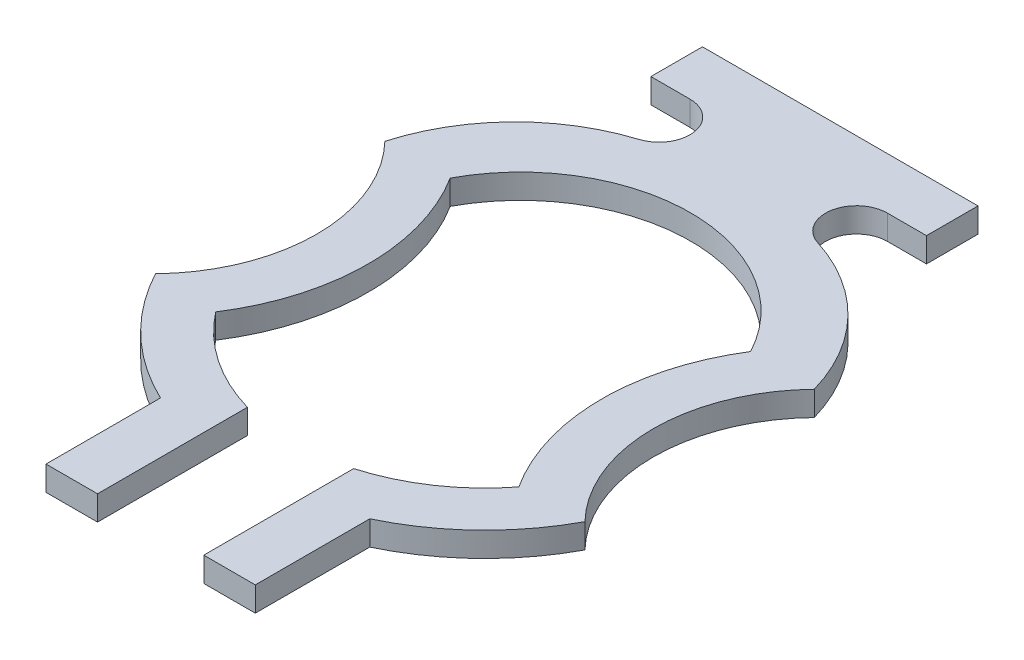
SolidWorks part; units mm, degrees
ref_plane "Alzado" through (0, 0, 0) normal (0, 0, 1) x (1, 0, 0)
ref_plane "Planta" through (0, 0, 0) normal (0, 1, 0) x (1, 0, 0)
ref_plane "Vista lateral" through (0, 0, 0) normal (1, 0, 0) x (0, 0, -1)
sketch "Sketch1" plane through (0, 0, 0) normal (0, 1, 0) x (1, 0, 0)
  line L0 (0.1624, -1000.9575) -> (0.1624, 48999.0425) construction
  line L1 (0.3199, -1000.9802) -> (0.3199, 48999.0198) construction
  line L2 (0.4212, -1001.0075) -> (0.4212, 48998.9925) construction
  line L3 (-999.2046, 1.0862) -> (49000.7954, 1.0862) construction
  line L4 (-999.3251, 0.9287) -> (49000.6749, 0.9287) construction
  line L5 (-0.4212, 1.0862) -> (0.4212, 1.0862)
  line L6 (0.4212, 1.0862) -> (0.4212, 0.9287)
  line L7 (-999.188, -1.0218) -> (49000.812, -1.0218) construction
  line L8 (-0.1624, -0.5636) -> (-0.1624, -1.0218)
  line L9 (-0.1624, -1.0218) -> (-0.3199, -1.0218)
  line L10 (-0.3199, -1.0218) -> (-0.3199, -0.6718)
  line L11 (0, -1000) -> (0, 49000) construction
  line L12 (-1000, 0) -> (49000, 0) construction
  line L13 (1.019, -1000.0419) -> (1.019, 48999.9581) construction
  line L14 (-1000, 0.1085) -> (49000, 0.1085) construction
  line L15 (0.1624, -0.5636) -> (0.1624, -1.0218)
  line L16 (0.1624, -1.0218) -> (0.3199, -1.0218)
  line L17 (0.3199, -1.0218) -> (0.3199, -0.6718)
  line L18 (-1000.0995, 0.1915) -> (48999.9005, 0.1915) construction
  line L19 (0.0995, -999.6898) -> (0.0995, 49000.3102) construction
  line L20 (0.3019, 0.9287) -> (0.4212, 0.9287)
  line L21 (-0.3019, 0.9287) -> (-0.4212, 0.9287)
  line L22 (-0.4212, 1.0862) -> (-0.4212, 0.9287)
  arc A0 (-0.4592, 0.3532) -> (-0.4633, -0.3596) centre (-1.019, 0) cw
  arc A1 (-0.1624, -0.5636) -> (-0.4633, -0.3596) centre (0, 0) cw
  arc A2 (0.6563, 0.3506) -> (0.6563, -0.3506) centre (1.019, 0) ccw
  arc A3 (0.3019, 0.9287) -> (0.2734, 0.7439) centre (0.3019, 0.8341) ccw
  arc A4 (0.4592, 0.3532) -> (-0.4592, 0.3532) centre (0, 0.1085) ccw
  arc A5 (0.1624, -0.5636) -> (0.4633, -0.3596) centre (0, 0) ccw
  arc A6 (0.3199, -0.6718) -> (0.6563, -0.3506) centre (0, 0) ccw
  arc A7 (0.6563, 0.3506) -> (0.2734, 0.7439) centre (0.0995, 0.1915) ccw
  arc A8 (-0.3199, -0.6718) -> (-0.6563, -0.3506) centre (0, 0) cw
  arc A9 (-0.6563, 0.3506) -> (-0.6563, -0.3506) centre (-1.019, 0) cw
  arc A10 (-0.6563, 0.3506) -> (-0.2734, 0.7439) centre (-0.0995, 0.1915) cw
  arc A11 (-0.3019, 0.9287) -> (-0.2734, 0.7439) centre (-0.3019, 0.8341) cw
  arc A13 (0.4592, 0.3532) -> (0.4633, -0.3596) centre (1.019, 0) ccw
  point P21 (1.019, 0)
  point P55 (0.0995, 0.1915)
  point P59 (0, 1.0862)
  dimension "D3" = 0.5865
  dimension "D4" = 0.7441
  dimension "D5" = 0.1624
  dimension "D6" = 0.3199
  dimension "D7" = 0.5044
  dimension "D8" = 0.4212
  dimension "D9" = 1.0218
  dimension "D10" = 1.0862
  dimension "D12" = 0.9287
  dimension "D13" = 1.019
  dimension "D15" = 0.5791
  dimension "D18" = 0.5203
  dimension "D25" = 0.6619
  dimension "D27" = 0.1892
  dimension "D17" = 0.1085
  dimension "D21" = 0.1915
  dimension "D23" = 0.0995
extrude "Boss-Extrude1" add sketch "Sketch1" along normal blind 0.075
